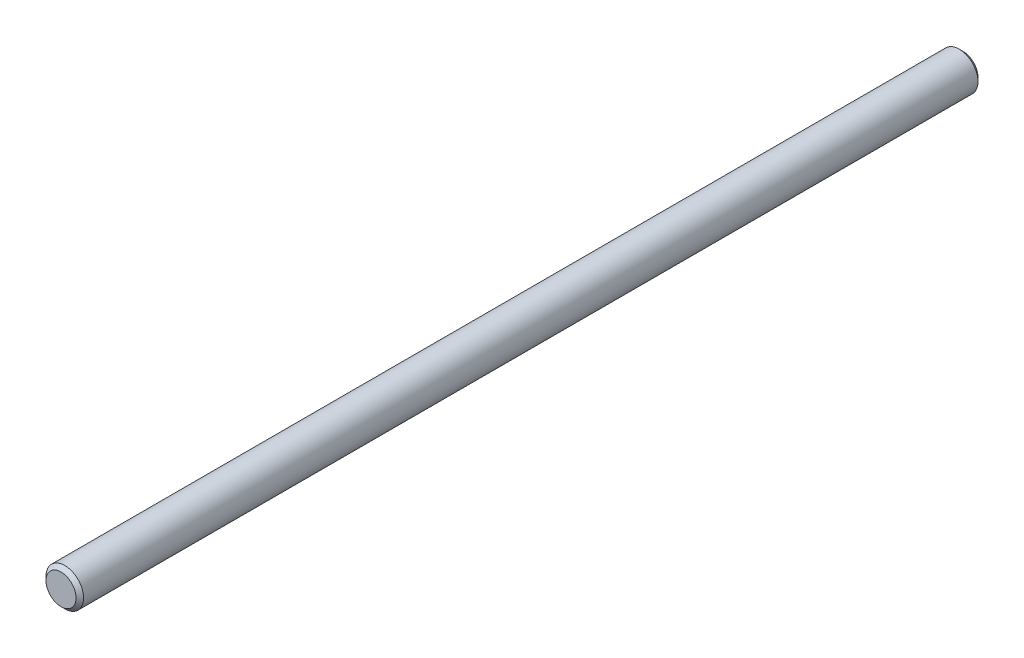
SolidWorks part; units mm, degrees
material "1023 Carbon Steel Sheet (SS)"
ref_plane "Front" through (0, 0, 0) normal (0, 0, 1) x (1, 0, 0)
ref_plane "Top" through (0, 0, 0) normal (0, 1, 0) x (1, 0, 0)
ref_plane "Right" through (0, 0, 0) normal (1, 0, 0) x (0, 0, -1)
sketch "Sketch1" plane through (0, 0, 0) normal (0, 0, 1) x (1, 0, 0)
  circle A0 centre (0, 0) radius 6.35
  dimension "dia" = 12.7
extrude "Extrude1" add sketch "Sketch1" along normal mid plane 304.8
sketch "Sketch2" plane through (0, 0, 0) normal (1, 0, 0) x (0, 0, -1)
  point P0 (-152.4, 6.35)
  point P1 (152.4, 6.35)
chamfer "Chamfer1" distance 1.27 angle 45 2 edges at (6.35, 0, -152.4) (6.35, 0, 152.4)
equation "\"D1@Chamfer1\" = \"dia@Sketch1\" * .1"
